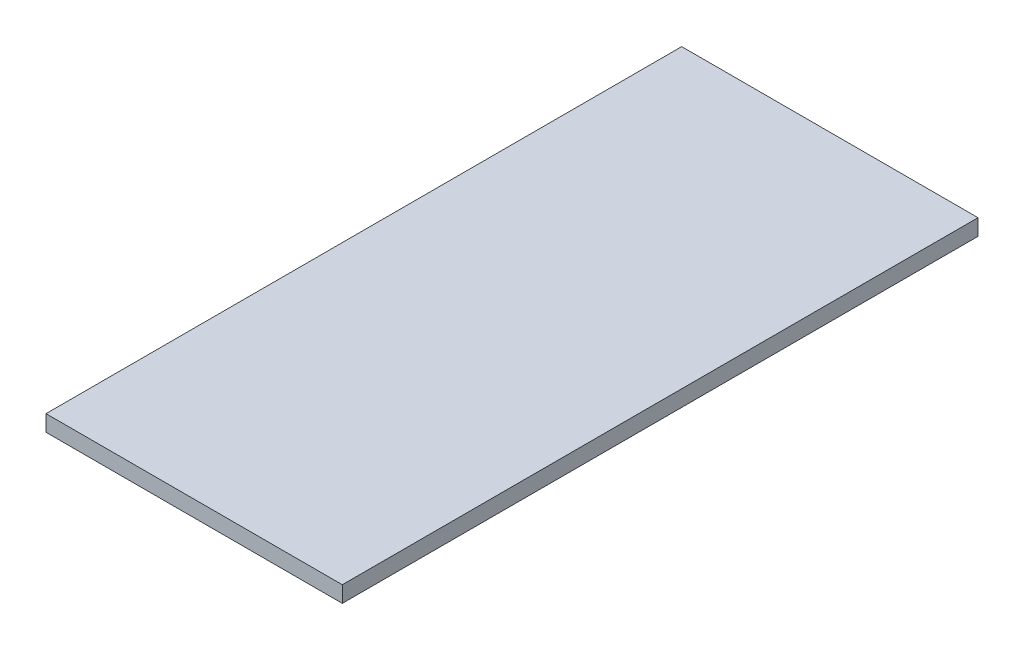
SolidWorks part; units mm, degrees
ref_plane "Front Plane" through (0, 0, 0) normal (0, 0, 1) x (1, 0, 0)
ref_plane "Top Plane" through (0, 0, 0) normal (0, 1, 0) x (1, 0, 0)
ref_plane "Right Plane" through (0, 0, 0) normal (1, 0, 0) x (0, 0, -1)
sketch "Sketch1" plane through (0, 0, 0) normal (0, 1, 0) x (1, 0, 0)
  line L1 (-27.5, -59) -> (27.5, -59)
  line L2 (-27.5, -59) -> (-27.5, 59)
  line L3 (-27.5, 59) -> (27.5, 59)
  line L4 (27.5, -59) -> (27.5, 59)
  line L5 (-27.5, -59) -> (27.5, 59) construction
  line L6 (-27.5, 59) -> (27.5, -59) construction
  point P0 (0, 0)
  point P16 (16.5832, -56.7278)
  dimension "D1" = 118
  dimension "D2" = 55
extrude "Boss-Extrude1" add sketch "Sketch1" along normal blind 3
